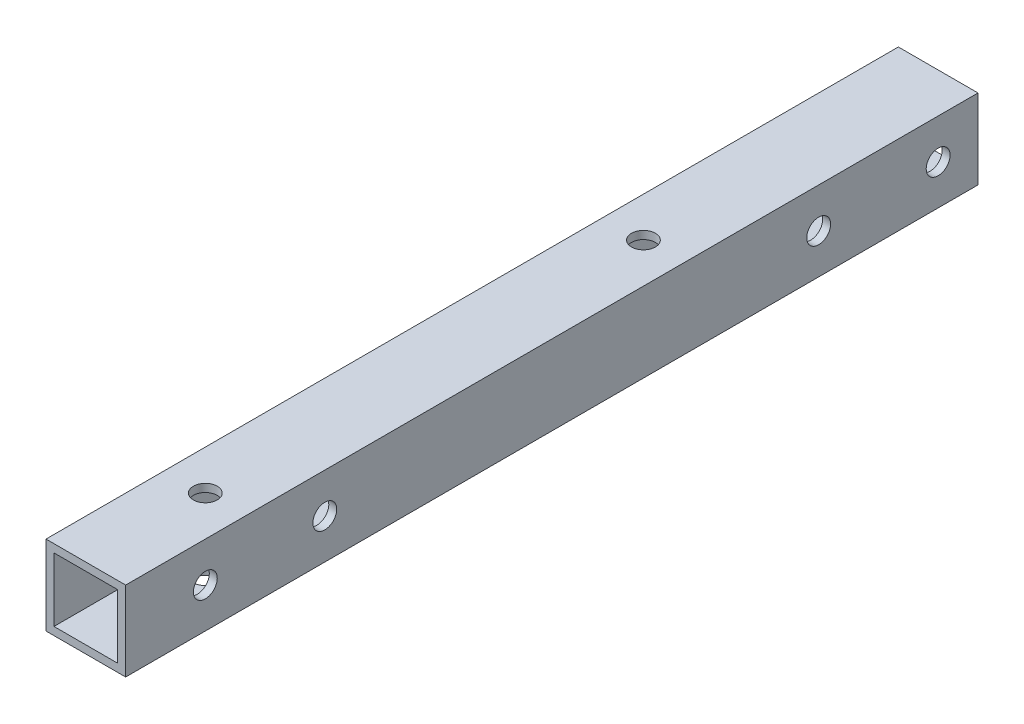
SolidWorks part; units mm, degrees
material "6063-O"
ref_plane "前视基准面" through (0, 0, 0) normal (0, 0, 1) x (1, 0, 0)
ref_plane "上视基准面" through (0, 0, 0) normal (0, 1, 0) x (1, 0, 0)
ref_plane "右视基准面" through (0, 0, 0) normal (1, 0, 0) x (0, 0, -1)
other "Configuration Table"
sketch "草图1" plane through (0, 0, 0) normal (0, 0, 1) x (1, 0, 0)
  line L1 (-5, -5) -> (5, -5)
  line L2 (-5, -5) -> (-5, 5)
  line L3 (-5, 5) -> (5, 5)
  line L4 (5, -5) -> (5, 5)
  line L5 (-5, -5) -> (5, 5) construction
  line L6 (-5, 5) -> (5, -5) construction
  point P4 (0, 0)
  dimension "D1" = 10
  dimension "D2" = 10
extrude "拉伸-薄壁1" add sketch "草图1" along normal blind 107 thin thin type one direction reverse wall 1
sketch "草图2" plane through (5, 0, 0) normal (1, 0, 0) x (0, 0, -1)
  line L0 (0, 0) -> (-107, 0) construction
  line L1 (-107, -5) -> (-107, 5) construction
  circle A0 centre (-5, 0) radius 1.5
  circle A1 centre (-20, 0) radius 1.5
  circle A2 centre (-97, 0) radius 1.5
  circle A3 centre (-82, 0) radius 1.5
  dimension "D1" = 3
  dimension "D3" = 15
  dimension "D4" = 10
  dimension "D5" = 15
  dimension "D2" = 5
extrude "切除-拉伸1" cut sketch "草图2" against normal through all
sketch "草图3" plane through (0, -5, 0) normal (0, -1, 0) x (1, 0, 0)
  line L0 (0, 107) -> (0, 49.8065) construction
  line L1 (-5, 107) -> (5, 107) construction
  circle A0 centre (0, 92) radius 1.5
  circle A1 centre (0, 37) radius 1.5
  dimension "D1" = 3
  dimension "D2" = 55
  dimension "D3" = 15
extrude "切除-拉伸2" cut sketch "草图3" against normal blind 10
